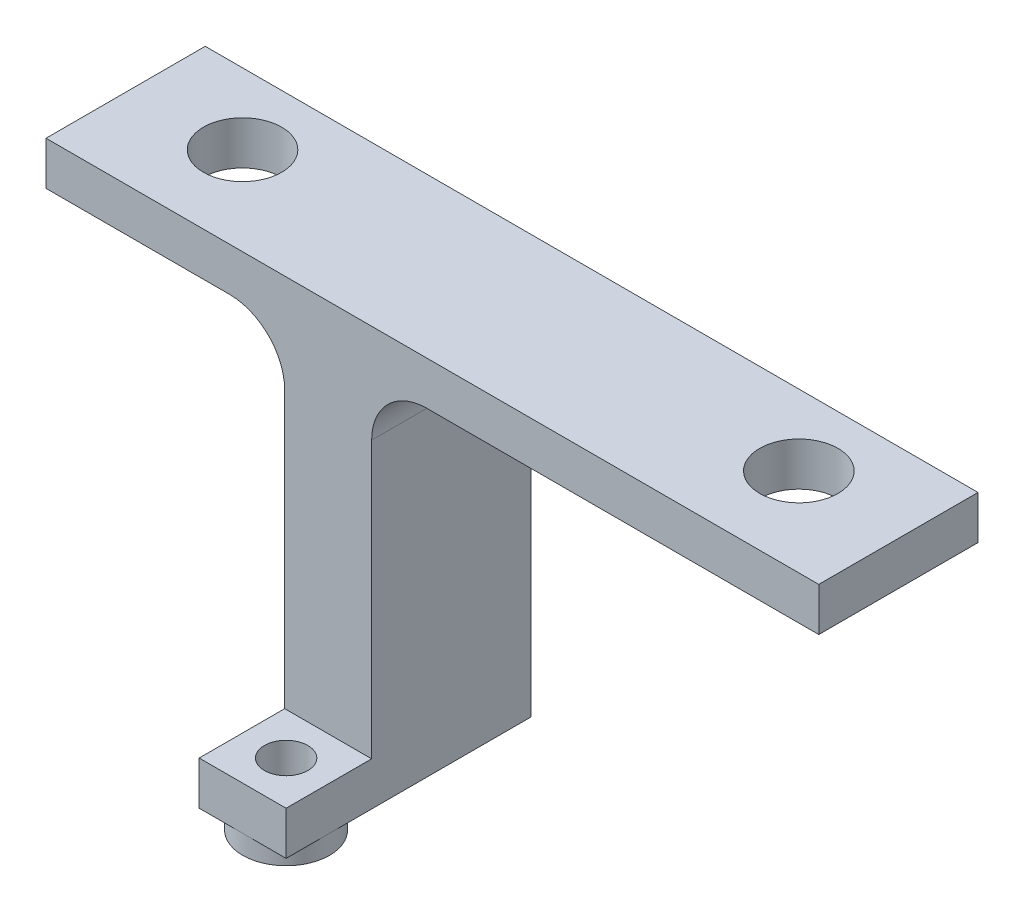
SolidWorks part; units mm, degrees
ref_plane "Front Plane" through (0, 0, 0) normal (0, 0, 1) x (1, 0, 0)
ref_plane "Top Plane" through (0, 0, 0) normal (0, 1, 0) x (1, 0, 0)
ref_plane "Right Plane" through (0, 0, 0) normal (1, 0, 0) x (0, 0, -1)
sketch "Sketch1" plane through (0, 0, 0) normal (0, 1, 0) x (1, 0, 0)
  line L1 (-22.225, -5.08) -> (22.225, -5.08)
  line L2 (-22.225, -5.08) -> (-22.225, 5.08)
  line L3 (-22.225, 5.08) -> (22.225, 5.08)
  line L4 (22.225, -5.08) -> (22.225, 5.08)
  line L5 (-22.225, -5.08) -> (22.225, 5.08) construction
  line L6 (-22.225, 5.08) -> (22.225, -5.08) construction
  circle A0 centre (-16, 0) radius 2.25
  circle A1 centre (16, 0) radius 2.25
  point P0 (0, 0)
  dimension "D1" = 4.5
  dimension "D2" = 44.45
  dimension "D3" = 10.16
  dimension "D4" = 32
  dimension "D5" = 16
extrude "Boss-Extrude1" add sketch "Sketch1" along normal blind 2.5
sketch "Sketch3" plane through (0, 0, 0) normal (0, -1, 0) x (-1, 0, 0)
  line L0 (22.225, -5.08) -> (-22.225, -5.08) construction
  line L1 (8.4944, 5.08) -> (3.4944, 5.08)
  line L2 (8.4944, 5.08) -> (8.4944, -5.08)
  line L3 (8.4944, -5.08) -> (3.4944, -5.08)
  line L4 (3.4944, 5.08) -> (3.4944, -5.08)
  line L5 (8.4944, 5.08) -> (3.4944, -5.08) construction
  line L6 (8.4944, -5.08) -> (3.4944, 5.08) construction
  line L7 (-22.225, 5.08) -> (22.225, 5.08) construction
  point P0 (5.9944, 0)
  point P8 (0, 0)
  point P9 (0, 2.0595)
  point P12 (2.0104, 0)
  dimension "D1" = 5
  dimension "D2" = 5.9944
extrude "Boss-Extrude2" add sketch "Sketch3" along direction (0, -1, 0) on the side of the normal blind 19.05
sketch "Sketch5" plane through (0, -19.05, 0) normal (0, -1, 0) x (1, 0, 0)
  line L0 (-3.4944, -5.08) -> (-3.4944, 5.08) construction
  line L1 (-8.4944, -10) -> (-3.4944, -10) construction
  line L2 (-8.4944, -10) -> (-8.4944, 10) construction
  line L3 (-8.4944, 10) -> (-3.4944, 10)
  line L4 (-3.4944, -10) -> (-3.4944, 10) construction
  line L5 (-8.4944, -10) -> (-3.4944, 10) construction
  line L6 (-8.4944, 10) -> (-3.4944, -10) construction
  line L7 (-8.4944, -5.08) -> (-3.4944, -5.08) construction
  line L8 (-8.4944, -5.08) -> (-3.4944, -5.08)
  line L9 (-8.4944, 10) -> (-8.4944, -5.08)
  line L10 (-3.4944, 10) -> (-3.4944, -5.08)
  line L11 (-8.4944, 5.08) -> (-8.4944, -5.08) construction
  circle A0 centre (-5.9944, 7.5) radius 1.25
  point P0 (-5.9944, 0)
  point P22 (0, 0)
  dimension "D2" = 2.5
  dimension "D1" = 20
  dimension "D3" = 2.5
extrude "Boss-Extrude3" add sketch "Sketch5" along normal blind 2.5
sketch "Sketch6" plane through (0, -21.55, 0) normal (0, -1, 0) x (1, 0, 0)
  line L0 (-3.4944, 10) -> (-8.4944, 10) construction
  circle A0 centre (-5.9944, 7.5) radius 1.25 construction
  circle A1 centre (-5.9944, 7.5) radius 1.25
  circle A2 centre (-5.9944, 7.5) radius 2.5
extrude "Boss-Extrude4" add sketch "Sketch6" along normal blind 1.1
fillet "Fillet1" radius 3.175 2 edges at (-8.4944, 0, 0) (-3.4944, 0, 0)
sketch "Sketch7" plane through (0, 0, -5.08) normal (0, 0, -1) x (-1, 0, 0)
  line L8 (-22.225, 0) -> (0.3194, 0)
  line L9 (3.4944, -3.175) -> (3.4944, -21.55)
  line L10 (3.4944, -21.55) -> (8.4944, -21.55)
  line L11 (8.4944, -21.55) -> (8.4944, -3.175)
  line L12 (11.6694, 0) -> (22.225, 0)
  line L13 (22.225, 0) -> (22.225, 2.5)
  line L14 (22.225, 2.5) -> (-22.225, 2.5)
  line L15 (-22.225, 2.5) -> (-22.225, 0)
  line L16 (-22.225, 0) -> (0.3194, 0)
  line L17 (3.4944, -3.175) -> (3.4944, -21.55)
  line L19 (8.4944, -21.55) -> (8.4944, -3.175)
  line L20 (11.6694, 0) -> (22.225, 0)
  line L21 (22.225, 0) -> (22.225, 2.5)
  line L22 (22.225, 2.5) -> (-22.225, 2.5)
  line L23 (-22.225, 2.5) -> (-22.225, 0)
  line L25 (3.4944, -21.55) -> (8.4944, -21.55)
  arc A2 (3.4944, -3.175) -> (0.3194, 0) centre (0.3194, -3.175) ccw
  arc A3 (11.6694, 0) -> (8.4944, -3.175) centre (11.6694, -3.175) ccw
  arc A4 (3.4944, -3.175) -> (0.3194, 0) centre (0.3194, -3.175) ccw
  arc A5 (11.6694, 0) -> (8.4944, -3.175) centre (11.6694, -3.175) ccw
  dimension "D1" = 0
extrude "Cut-Extrude1" cut sketch "Sketch7" against normal blind 1
